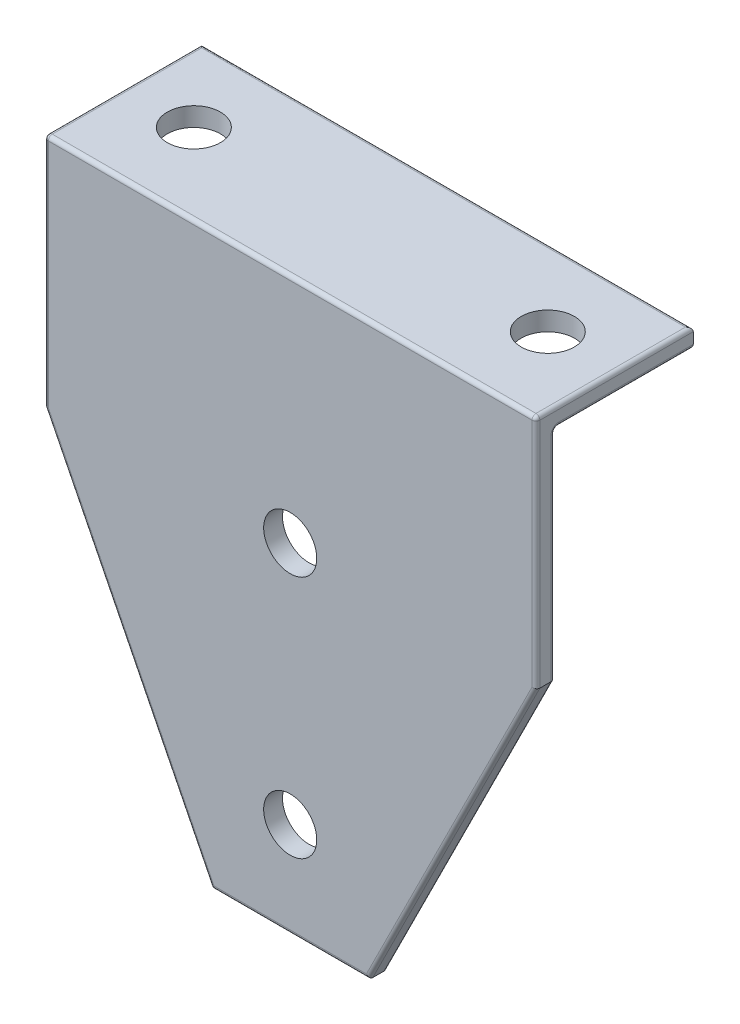
SolidWorks part; units mm, degrees
ref_plane "Alzado" through (0, 0, 0) normal (0, 0, 1) x (1, 0, 0)
ref_plane "Planta" through (0, 0, 0) normal (0, 1, 0) x (1, 0, 0)
ref_plane "Vista lateral" through (0, 0, 0) normal (1, 0, 0) x (0, 0, -1)
sketch "Croquis1" plane through (0, 0, 0) normal (0, 0, 1) x (1, 0, 0)
  line L2 (-912.5, -63.6) -> (-912.5, -123.6)
  line L4 (-787.5, -63.6) -> (-787.5, -123.6)
  line L5 (-912.5, -123.6) -> (-870, -208.6)
  line L6 (-870, -208.6) -> (-830, -208.6)
  line L7 (-830, -208.6) -> (-787.5, -123.6)
  line L8 (-912.5, -63.6) -> (-787.5, -63.6)
  line L9 (-991.0574, -63.6) -> (991.0574, -63.6) construction
  point P0 (-911.1793, -63.6)
  point P3 (-850, -63.6)
  point P7 (-850, -208.6)
  dimension "D1" = 60
  dimension "D2" = 145
  dimension "D3" = 40
  dimension "D4" = 125
  dimension "D5" = 12.5
extrude "Saliente-Extruir1" add sketch "Croquis1" against normal blind 4.8
sketch "Croquis2" plane through (0, 0, -4.8) normal (0, 0, -1) x (-1, 0, 0)
  line L0 (912.5, -63.6) -> (912.5, -123.6) construction
  line L1 (787.5, -63.6) -> (912.5, -63.6)
  line L2 (787.5, -63.6) -> (787.5, -68.4)
  line L3 (787.5, -68.4) -> (912.5, -68.4)
  line L4 (912.5, -63.6) -> (912.5, -68.4)
  dimension "D1" = 4.8
extrude "Saliente-Extruir2" add sketch "Croquis2" along normal blind 35.2
fillet "Redondeo1" radius 1 18 edges at (-787.5, -68.4, -22.4) (-850, -68.4, -40) (-912.5, -68.4, -22.4) (-912.5, -63.6, -20) (-850, -63.6, -40) (-787.5, -63.6, -20) (-850, -208.6, 0) (-891.25, -166.1, 0) (-912.5, -93.6, 0) (-850, -63.6, 0) (-787.5, -93.6, 0) (-808.75, -166.1, 0) (-912.5, -96, -4.8) (-891.25, -166.1, -4.8) (-850, -208.6, -4.8) (-808.75, -166.1, -4.8) (-787.5, -96, -4.8) (-850, -68.4, -4.8)
sketch "Croquis4" plane through (0, -63.6, 0) normal (0, 1, 0) x (1, 0, 0)
  line L0 (-850, 40) -> (-850, 0) construction
  line L1 (-912.5, 40) -> (-787.5, 40) construction
  line L2 (-788.5, 0) -> (-911.5, 0) construction
  line L3 (-912.5, 20.5) -> (-787.5, 20.5) construction
  line L4 (-912.5, 1) -> (-912.5, 40) construction
  line L5 (-787.5, 40) -> (-787.5, 1) construction
  point P0 (-895, 20.5)
  point P1 (-805, 20.5)
  point P14 (-800.1302, 15.7385)
  point P15 (0, 0)
  point P16 (0, 0)
  dimension "D1" = 90
hole_wizard "Taladro de margen para M121" positions "Croquis4" profile "Croquis5" hole size "M12" standard "Ansi Metric" end condition through all
sketch "Croquis5" plane through (-895, -63.6, -20.5) normal (1, 0, 0) x (0, 0, 1)
  line L0 (0, 0) -> (0, 145)
  line L1 (0, 145) -> (6.75, 145)
  line L2 (6.75, 145) -> (6.75, 0)
  line L5 (6.75, 0) -> (0, 0)
  line L11 (0, -6.35) -> (0, 107.95) construction
  dimension "Diámetro de taladro hasta el siguiente" = 13.5
  dimension "Profundidad de taladro hasta el siguiente" = 145
sketch "Croquis6" plane through (0, 0, 0) normal (0, 0, 1) x (1, 0, 0)
  point P0 (-850, -122.4)
  point P1 (-850, -184.4)
hole_wizard "Taladro de margen para M122" positions "Croquis6" profile "Croquis7" hole size "M12" standard "Ansi Metric" end condition through all
sketch "Croquis7" plane through (-850, -122.4, 0) normal (1, 0, 0) x (0, -1, 0)
  line L0 (0, 0) -> (0, 40)
  line L1 (0, 40) -> (6.75, 40)
  line L2 (6.75, 40) -> (6.75, 0)
  line L5 (6.75, 0) -> (0, 0)
  line L11 (0, -6.35) -> (0, 107.95) construction
  dimension "Diámetro de taladro hasta el siguiente" = 13.5
  dimension "Profundidad de taladro hasta el siguiente" = 40
